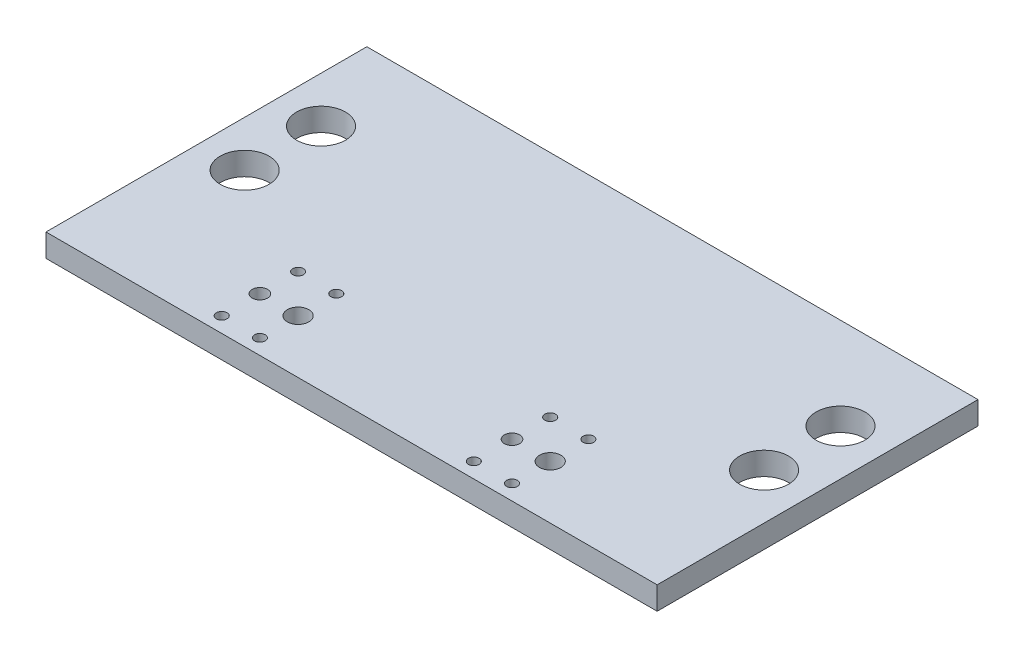
SolidWorks part; units mm, degrees
material "PBT Общее назначение"
ref_plane "Спереди" through (0, 0, 0) normal (0, 0, 1) x (1, 0, 0)
ref_plane "Сверху" through (0, 0, 0) normal (0, 1, 0) x (1, 0, 0)
ref_plane "Справа" through (0, 0, 0) normal (1, 0, 0) x (0, 0, -1)
sketch "Эскиз1" plane through (0, 0, 0) normal (0, 1, 0) x (1, 0, 0)
  line L0 (0, 0) -> (40, 0)
  line L3 (0, 21) -> (40, 21)
  line L4 (40, 0) -> (40, 21)
  line L5 (0, 0) -> (0, 21)
  point P1 (40, 21)
  point P2 (0, 21)
  dimension "D1" = 21
  dimension "D2" = 40
extrude "Бобышка-Вытянуть1" add sketch "Эскиз1" along normal blind 1.5
sketch "Эскиз2" plane through (0, 1.5, 0) normal (0, 1, 0) x (1, 0, 0)
  line L0 (0, 21) -> (0, 0) construction
  line L1 (0, 21) -> (0, 0) construction
  line L4 (0, 0) -> (40, 0) construction
  line L5 (0, 0) -> (40, 0) construction
  circle A0 centre (29.5, 3.5) radius 0.7
  circle A1 centre (27, 3.5) radius 0.5
  circle A2 centre (13, 3.5) radius 0.7
  circle A3 centre (10.5, 3.5) radius 0.5
  circle A4 centre (27, 6) radius 0.35
  circle A5 centre (29.5, 6) radius 0.35
  circle A6 centre (29.5, 1) radius 0.35
  circle A7 centre (27, 1) radius 0.35
  circle A8 centre (13, 6) radius 0.35
  circle A9 centre (10.5, 6) radius 0.35
  circle A10 centre (10.5, 1) radius 0.35
  circle A11 centre (13, 1) radius 0.35
  circle A12 centre (3, 10) radius 1.6
  circle A13 centre (37, 10) radius 1.6
  circle A14 centre (3, 15) radius 1.6
  circle A15 centre (37, 15) radius 1.6
  dimension "D2" = 34
  dimension "D3" = 16.5
  dimension "D4" = 0
  dimension "D5" = 1.4
  dimension "D6" = 1
  dimension "D7" = 10.5
  dimension "D8" = 3.5
  dimension "D9" = 2.5
  dimension "D10" = 2.5
  dimension "D11" = 0.7
  dimension "D12" = 2.5
  dimension "D13" = 2.5
  dimension "D14" = 5
  dimension "D15" = 5
  dimension "D16" = 3
  dimension "D17" = 10
  dimension "D18" = 3.2
  dimension "D19" = 5
extrude "Вырез-Вытянуть1" cut sketch "Эскиз2" against normal through all
